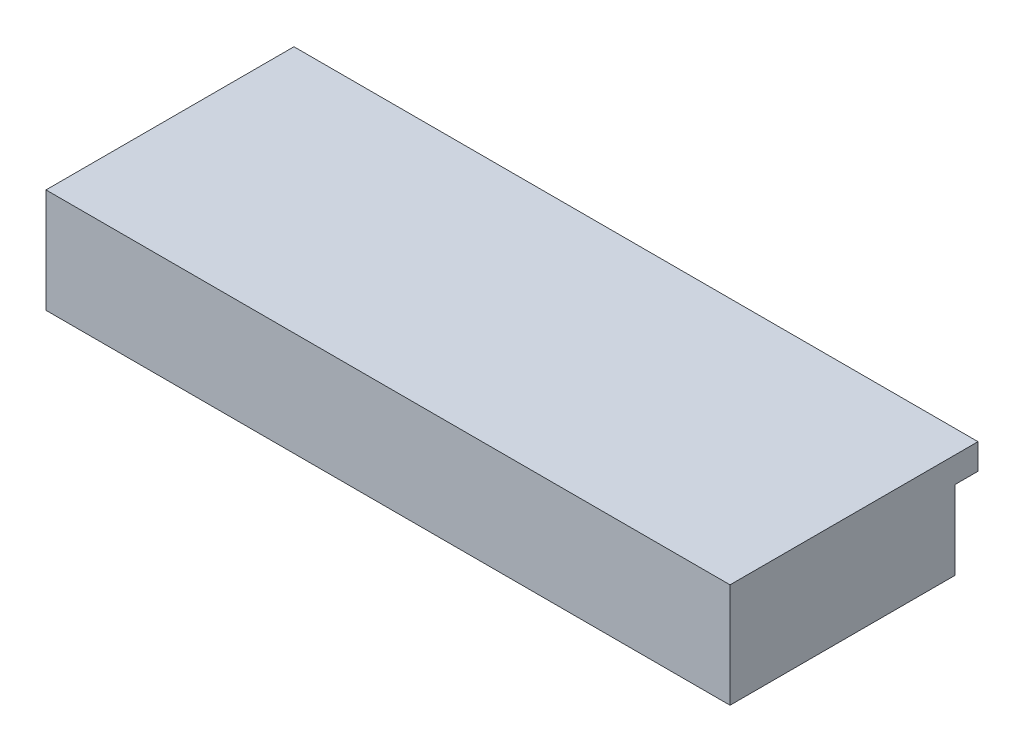
SolidWorks part; units mm, degrees
ref_plane "Plan de face" through (0, 0, 0) normal (0, 0, 1) x (1, 0, 0)
ref_plane "Plan de dessus" through (0, 0, 0) normal (0, 1, 0) x (1, 0, 0)
ref_plane "Plan de droite" through (0, 0, 0) normal (1, 0, 0) x (0, 0, -1)
sketch "Esquisse2" plane through (0, 0, 0) normal (0, 0, 1) x (1, 0, 0)
  line L0 (238, -21) -> (70.5, -21)
  line L1 (-59.5, -21) -> (-162, -21)
  line L2 (68.5, -21) -> (-57.5, -21) construction
  line L4 (238, 25) -> (-162, 25)
  line L5 (-162, 25) -> (-162, -15)
  line L6 (83, 19) -> (-70.25, 19)
  line L7 (-70.25, -6) -> (-61.5, -6)
  line L8 (-59.5, -8) -> (-59.5, -19)
  line L9 (-57.5, -21) -> (68.5, -21)
  line L10 (70.5, -19) -> (70.5, -8)
  line L11 (72.5, -6) -> (83, -6)
  line L12 (83, 19) -> (-70.25, 19)
  line L13 (-70.25, -6) -> (-61.5, -6)
  line L14 (-59.5, -8) -> (-59.5, -21)
  line L16 (70.5, -21) -> (70.5, -8)
  line L17 (72.5, -6) -> (83, -6)
  line L18 (-162, -15) -> (238, -15)
  line L19 (238, -15) -> (238, 25)
  line L20 (238, 25) -> (-162, 25)
  line L21 (-162, 25) -> (-162, -21)
  line L23 (238, -21) -> (238, 25)
  arc A6 (83, -6) -> (83, 19) centre (83, 6.5) ccw
  arc A7 (-70.25, 19) -> (-70.25, -6) centre (-70.25, 6.5) ccw
  arc A8 (-59.5, -8) -> (-61.5, -6) centre (-61.5, -8) ccw
  arc A9 (-59.5, -19) -> (-57.5, -21) centre (-57.5, -19) ccw
  arc A10 (68.5, -21) -> (70.5, -19) centre (68.5, -19) ccw
  arc A11 (72.5, -6) -> (70.5, -8) centre (72.5, -8) ccw
  arc A12 (83, -6) -> (83, 19) centre (83, 6.5) ccw
  arc A13 (-70.25, 19) -> (-70.25, -6) centre (-70.25, 6.5) ccw
  arc A14 (-59.5, -8) -> (-61.5, -6) centre (-61.5, -8) ccw
  arc A17 (72.5, -6) -> (70.5, -8) centre (72.5, -8) ccw
  dimension "D1" = 0
  dimension "D2" = 0
extrude "Extrusion1" add sketch "Esquisse2" against normal up to surface (1.5 mm away)
sketch "Esquisse3" plane through (0, 0, 0) normal (0, 0, 1) x (1, 0, 0)
  line L0 (238, -21) -> (238, 25) construction
  line L1 (238, -21) -> (238, 25)
  line L2 (238, 25) -> (-162, 25) construction
  line L3 (238, 25) -> (-162, 25)
  line L4 (70.5, -21) -> (238, -21) construction
  line L5 (-162, -21) -> (238, -21)
  line L6 (-162, 25) -> (-162, -21) construction
  line L7 (-162, 25) -> (-162, -21)
extrude "Extrusion2" add sketch "Esquisse3" along normal blind 130
sketch "Esquisse4" plane through (0, 0, 130) normal (0, 0, 1) x (1, 0, 0)
  line L0 (-162, 25) -> (-162, -21) construction
  line L1 (238, 25) -> (-162, 25)
  line L2 (238, 25) -> (238, 40)
  line L3 (238, 40) -> (-162, 40)
  line L4 (-162, 25) -> (-162, 40)
  dimension "D1" = 15
extrude "Extrusion3" add sketch "Esquisse4" against normal blind 145
